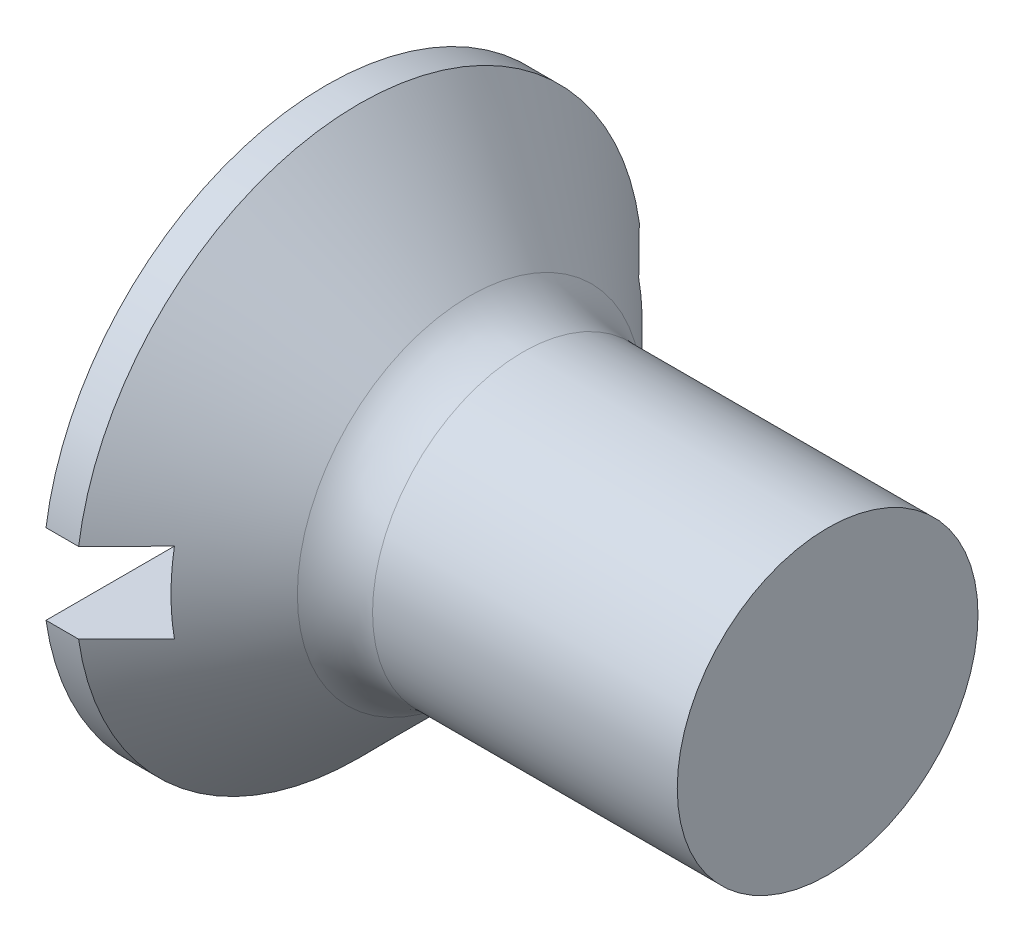
SolidWorks part; units mm, degrees
ref_plane "Plane1" through (0, 0, 0) normal (0, 0, 1) x (1, 0, 0)
ref_plane "Plane2" through (0, 0, 0) normal (0, 1, 0) x (1, 0, 0)
ref_plane "Plane3" through (0, 0, 0) normal (1, 0, 0) x (0, 0, -1)
sketch "BodySke" plane through (0, 0, 0) normal (0, 0, 1) x (1, 0, 0)
  line L0 (0, 0) -> (0, 5.65)
  line L1 (0, 5.65) -> (0.65, 5.65)
  line L2 (3.3, 3) -> (10, 3)
  line L3 (10, 3) -> (10, 0)
  line L4 (10, 0) -> (0, 0)
  line L5 (-6.35, 0) -> (82.55, 0) construction
  line L6 (3.3, -3) -> (10, -3) construction
  line L7 (0.65, -5.65) -> (3.3, -3) construction
  line L8 (0.65, 5.65) -> (3.3, 3)
  line L9 (0, -5.65) -> (0.65, -5.65) construction
  line L10 (4.3, 4.5875) -> (4.3, -4.9375) construction
  line L11 (0, 6.35) -> (0, -3.175) construction
  dimension "Diameter" = 6
  dimension "Length" = 10
  dimension "Head_ht" = 3.3
  dimension "Head_dia" = 11.3
  dimension "Head_ang" = 90
  dimension "D6" = 0.65
  dimension "Advance" = 1
  dimension "Thread_nom" = 10
revolve "Base-Revolve" add sketch "BodySke" angle 360 about L5
cosmetic thread "ThreadCosmetic" parameters "Thread_length"=5.7, "Thread_minor"=4.891
fillet "Fillet1" radius 1.5 1 edges at (3.3, 0, 3)
sketch "Sketch2" plane through (0, 0, 0) normal (-1, 0, 0) x (0, 0, 1)
  line L0 (-5.65, -0.8) -> (5.65, -0.8)
  line L1 (-5.65, -0.8) -> (-5.65, 0.8)
  line L2 (5.65, 0.8) -> (-5.65, 0.8)
  line L3 (5.65, 0.8) -> (5.65, -0.8)
  dimension "D1" = 0.8
  dimension "Slot_width" = 1.6
  dimension "D2" = 11.3
  dimension "D3" = 5.65
extrude "Slot" cut sketch "Sketch2" against normal blind 1.6
sketch "ThdSchSke" plane through (0, 0, 0) normal (0, 0, 1) x (1, 0, 0)
  line L0 (4.3, -2.4455) -> (3.9117, -3)
  line L1 (4.3, -2.4455) -> (4.6883, -3)
  line L2 (4.6883, -3) -> (4.6883, -3.75)
  line L3 (-3.175, 0) -> (5.1513, 0) construction
  line L5 (4.6883, -3.75) -> (3.9117, -3.75)
  line L6 (3.9117, -3.75) -> (3.9117, -3)
  line L7 (0, 5.65) -> (0, 0.8) construction
  dimension "Thread_minor" = 4.891
  dimension "Diameter" = 6
  dimension "Start" = 4.3
  dimension "SideAngle" = 55
  dimension "VeeAngle" = 70
  dimension "Overcut" = 7.5
revolve "ThreadSchematic" [suppressed] cut sketch "ThdSchSke" angle 360 about L3
pattern_linear "ThdSchPat" [suppressed]
equation "\"D1@Sketch2\" = \"Slot_width@Sketch2\" / 2"
equation "\"D2@Sketch2\" = \"Head_dia@BodySke\""
equation "\"D3@Sketch2\" = \"D2@Sketch2\" / 2"
equation "\"Thread_length@ThreadCosmetic\" = ((sgn( (\"Length@BodySke\" - \"Advance@BodySke\" * 1.0 - \"Head_ht@BodySke\" ) - \"Thread_nom@BodySke\" )-1)*( (\"Length@BodySke\" - \"Advance@BodySke\" * 1.0 - \"Head_ht@BodySke\" ) - \"Thread_nom@BodySke\" ))/-2+ \"Thread_nom@BodySke\""
equation "\"Thread_minor@ThdSchSke\" = \"Thread_minor@ThreadCosmetic\""
equation "\"Diameter@ThdSchSke\" = \"Diameter@BodySke\""
equation "\"Overcut@ThdSchSke\" = \"Diameter@BodySke\" * 1.25"
equation "\"Start@ThdSchSke\" = 0.000001 + \"Length@BodySke\" - \"Thread_length@ThreadCosmetic\"  '---Countersunk---"
equation "\"Num_threads@ThdSchPat\" = int( \"Thread_length@ThreadCosmetic\" / \"Advance@BodySke\" + 0.999 )  + 1"
equation "\"Advance@ThdSchPat\" = \"Thread_length@ThreadCosmetic\" /  (\"Num_threads@ThdSchPat\" - 1) 'relax it"
